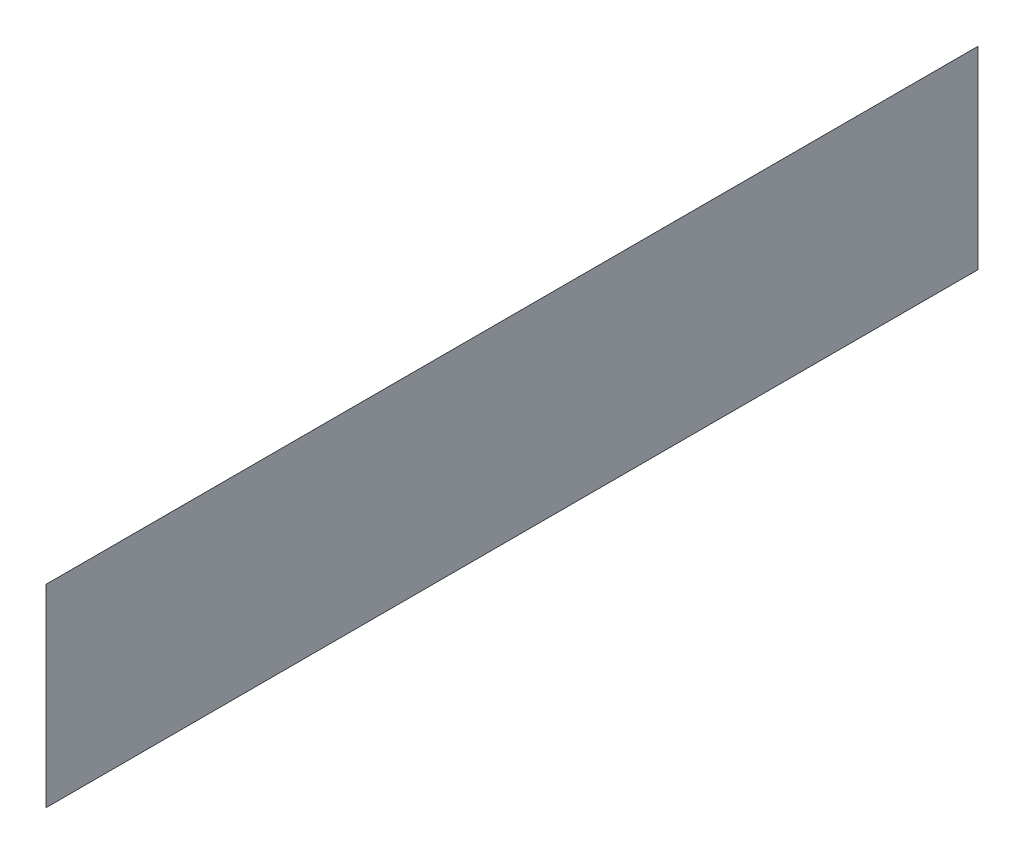
SolidWorks part; units mm, degrees
ref_plane "Front Plane" through (0, 0, 0) normal (0, 0, 1) x (1, 0, 0)
ref_plane "Top Plane" through (0, 0, 0) normal (0, 1, 0) x (1, 0, 0)
ref_plane "Right Plane" through (0, 0, 0) normal (1, 0, 0) x (0, 0, -1)
sketch "Sketch1" plane through (0, 0, 0) normal (0, 1, 0) x (1, 0, 0)
  line L0 (0, 244.7) -> (-32.9017, 211.7983)
  line L2 (-32.9017, 32.9017) -> (-32.9017, 211.7983)
  line L4 (0, 0) -> (0, 244.7)
  line L5 (0, 0) -> (-32.9017, 32.9017)
  point P0 (0, 0)
  dimension "D1" = 244.7
  dimension "D2" = 46.53
  dimension "D3" = 45
  dimension "D4" = 45
extrude "Boss-Extrude1" add sketch "Sketch1" along normal blind 32.9
sketch "Sketch2" plane through (0, 0, 0) normal (0, 0, 1) x (1, 0, 0)
  line L0 (0, 32.9) -> (-32.9017, 0)
  line L5 (-32.9017, 0) -> (-32.9017, 32.9)
  line L6 (-32.9017, 32.9) -> (0, 32.9)
  dimension "D1" = 46.5288
  dimension "D2" = 32.9
  dimension "D3" = 45.001
extrude "Cut-Extrude1" cut sketch "Sketch2" against normal blind 275.9
sketch "Sketch3" plane through (0, 0, 0) normal (0, -1, 0) x (1, 0, 0)
  line L0 (0, 0) -> (-32.9017, -32.9017)
  line L1 (-32.9017, -32.9017) -> (-32.9017, -211.7983)
  line L2 (-32.9017, -211.7983) -> (0, -244.7)
  line L3 (0, -244.7) -> (0, 0)
extrude "Boss-Extrude2" add sketch "Sketch3" along normal blind 17.9
